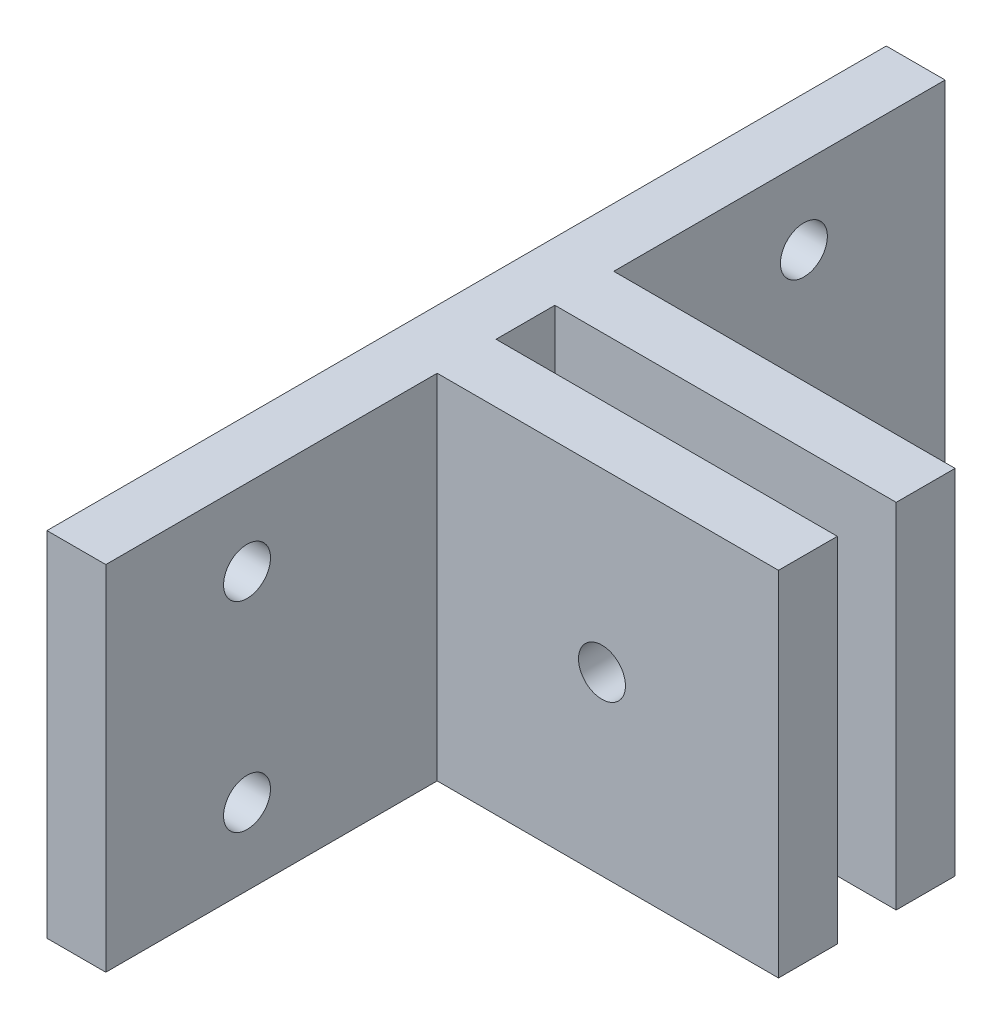
SolidWorks part; units mm, degrees
ref_plane "Front Plane" through (0, 0, 0) normal (0, 0, 1) x (1, 0, 0)
ref_plane "Top Plane" through (0, 0, 0) normal (0, 1, 0) x (1, 0, 0)
ref_plane "Right Plane" through (0, 0, 0) normal (1, 0, 0) x (0, 0, -1)
sketch "Sketch1" plane through (0, 0, 0) normal (0, 1, 0) x (1, 0, 0)
  line L0 (-35.248, 0) -> (69.7617, 0) construction
  line L1 (0, -22.6419) -> (0, 22.6419)
  line L2 (0, 22.6419) -> (3.175, 22.6419)
  line L3 (3.175, 22.6419) -> (3.175, 4.7625)
  line L4 (3.175, 4.7625) -> (21.59, 4.7625)
  line L5 (21.59, 4.7625) -> (21.59, 1.5875)
  line L6 (21.59, 1.5875) -> (3.175, 1.5875)
  line L7 (3.175, 1.5875) -> (3.175, -1.5875)
  line L8 (21.59, -4.7625) -> (21.59, -1.5875)
  line L9 (21.59, -1.5875) -> (3.175, -1.5875)
  line L10 (3.175, -4.7625) -> (21.59, -4.7625)
  line L11 (0, -22.6419) -> (3.175, -22.6419)
  line L12 (3.175, -22.6419) -> (3.175, -4.7625)
  point P3 (0, 0)
  point P14 (3.175, 0)
  point P17 (0, 0)
  dimension "D1" = 3.175
  dimension "D2" = 3.175
  dimension "D3" = 21.59
  dimension "D4" = 3.175
  dimension "D5" = 3.175
extrude "Boss-Extrude1" add sketch "Sketch1" along normal blind 19.05
sketch "Sketch2" plane through (0, 0, 4.7625) normal (0, 0, 1) x (1, 0, 0)
  line L0 (3.175, 19.05) -> (21.59, 19.05) construction
  line L4 (3.175, 19.05) -> (3.175, 0) construction
  circle A0 centre (12.065, 9.525) radius 1.2662
  dimension "D3" = 2.5324
  dimension "D1" = 9.525
  dimension "D2" = 8.89
extrude "Cut-Extrude1" cut sketch "Sketch2" against normal through all and the other way through all
sketch "Sketch3" plane through (3.175, 0, 0) normal (1, 0, 0) x (0, 0, -1)
  line L0 (0, 19.05) -> (0, 0) construction
  line L1 (-1.5875, 19.05) -> (1.5875, 19.05) construction
  line L2 (-22.6419, 9.525) -> (22.6419, 9.525) construction
  line L3 (-22.6419, 19.05) -> (-22.6419, 0) construction
  line L4 (22.6419, 19.05) -> (22.6419, 0) construction
  line L5 (-22.6419, 19.05) -> (-4.7625, 19.05) construction
  circle A0 centre (-15.0219, 14.9225) radius 1.2662
  circle A1 centre (-15.0219, 4.1275) radius 1.2662
  circle A2 centre (15.0219, 4.1275) radius 1.2662
  circle A3 centre (15.0219, 14.9225) radius 1.2662
  dimension "D3" = 2.5324
  dimension "D1" = 4.1275
  dimension "D2" = 7.62
extrude "Cut-Extrude2" cut sketch "Sketch3" against normal through all
